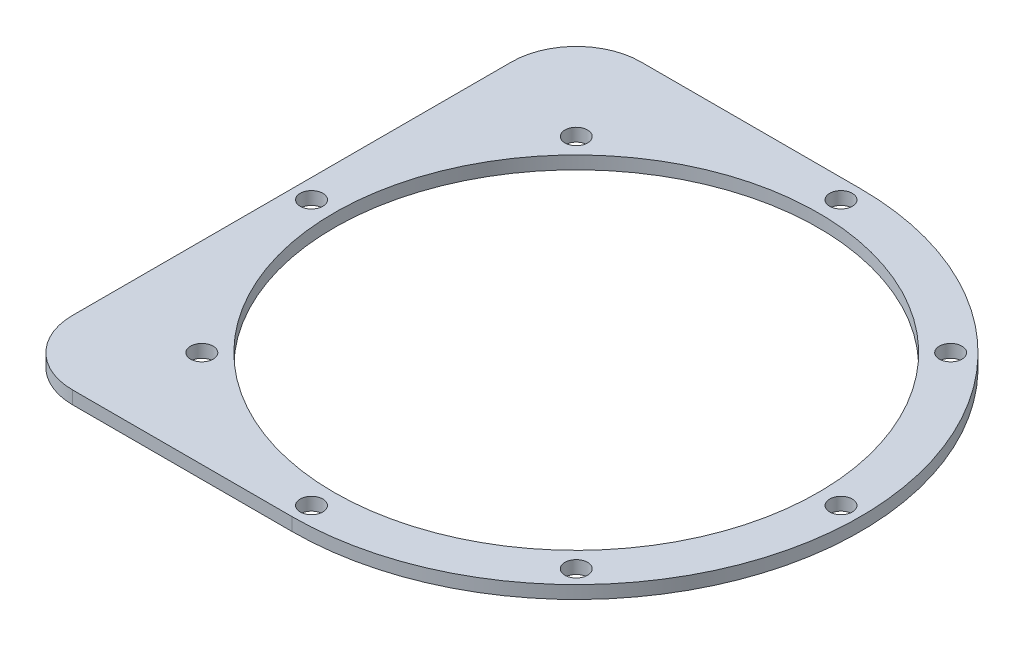
SolidWorks part; units mm, degrees
ref_plane "Front Plane" through (0, 0, 0) normal (0, 0, 1) x (1, 0, 0)
ref_plane "Top Plane" through (0, 0, 0) normal (0, 1, 0) x (1, 0, 0)
ref_plane "Right Plane" through (0, 0, 0) normal (1, 0, 0) x (0, 0, -1)
sketch "Sketch1" plane through (0, 0, 0) normal (0, 1, 0) x (1, 0, 0)
  circle A0 centre (0, 0) radius 44
  dimension "D1" = 88
extrude "Boss-Extrude1" add sketch "Sketch1" along normal blind 2
sketch "Sketch2" plane through (0, 2, 0) normal (0, 1, 0) x (1, 0, 0)
  line L1 (0, -44) -> (-44, -44)
  line L2 (0, -44) -> (0, 44)
  line L3 (0, 44) -> (-44, 44)
  line L4 (-44, -44) -> (-44, 44)
  line L5 (0, -44) -> (-44, 44) construction
  line L6 (0, 44) -> (-44, -44) construction
  circle A0 centre (0, 0) radius 44 construction
  point P0 (-22, 0)
extrude "Boss-Extrude2" add sketch "Sketch2" against normal up to surface (2 mm away) up to face at (0, 0, 44)
sketch "Sketch3" plane through (0, 2, 0) normal (0, 1, 0) x (1, 0, 0)
  circle A0 centre (41, 0) radius 1.75
  dimension "D1" = 3.5
  dimension "D2" = 41
extrude "Cut-Extrude1" cut sketch "Sketch3" against normal through all
pattern_circular "CirPattern1" count 8 over 360 about axis through (0, 0, 0) along (0, 1, 0) of "Cut-Extrude1"
sketch "Sketch4" plane through (0, 2, 0) normal (0, 1, 0) x (1, 0, 0)
  circle A0 centre (0, 0) radius 37.5
  dimension "D1" = 75
extrude "Cut-Extrude2" cut sketch "Sketch4" against normal through all
fillet "Fillet1" radius 10 2 edges at (-44, 1, 44) (-44, 1, -44)
